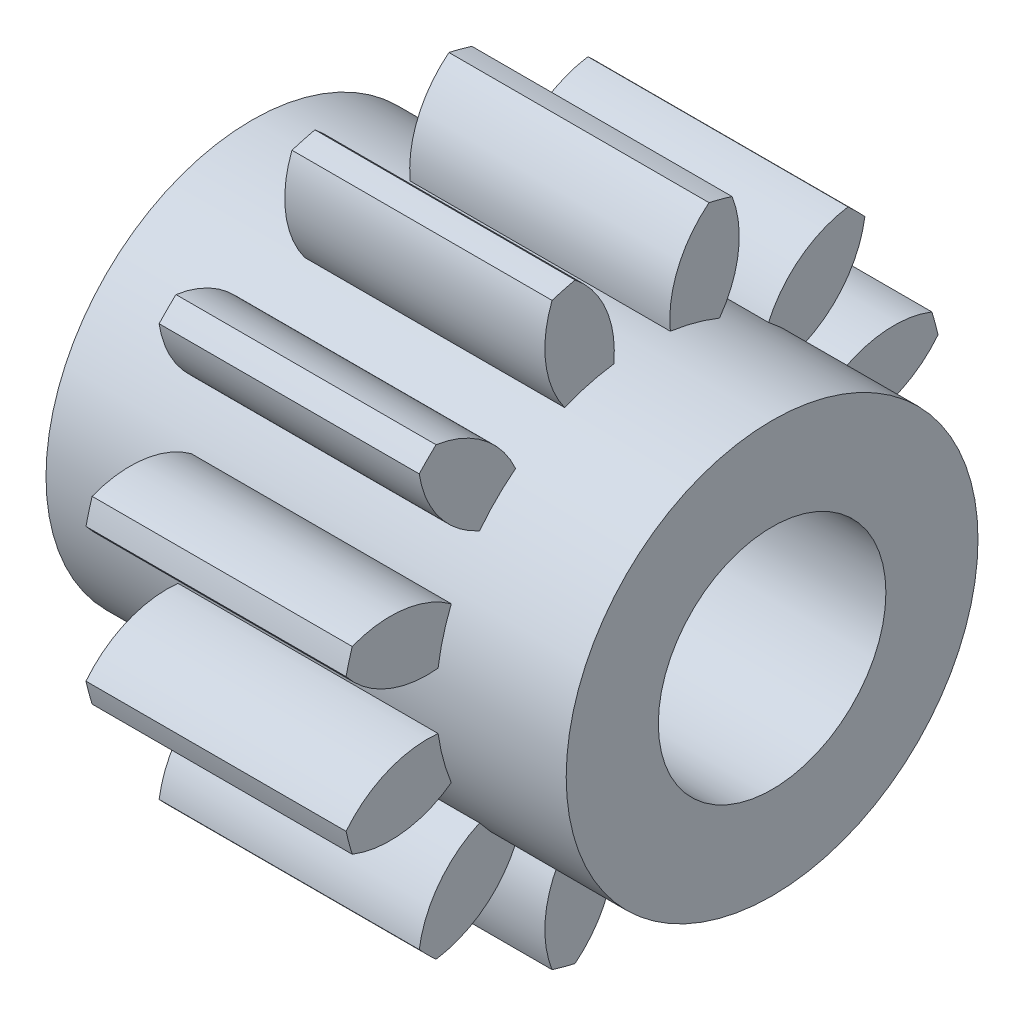
SolidWorks part; units mm, degrees
ref_plane "Plane1" through (0, 0, 0) normal (0, 0, 1) x (1, 0, 0)
ref_plane "Plane2" through (0, 0, 0) normal (0, 1, 0) x (1, 0, 0)
ref_plane "Plane3" through (0, 0, 0) normal (1, 0, 0) x (0, 0, -1)
sketch "HoldingSke" plane through (0, 0, 0) normal (0, 1, 0) x (1, 0, 0)
  line L0 (0, 0) -> (149.0697, -31.6857)
  line L1 (-15, 0) -> (100, 0) construction
  line L2 (0, 0) -> (-2.1039, 2.3779)
  line L3 (0, 0) -> (-11.863, 4.5341)
  line L4 (0, 0) -> (8.4473, 1.7955)
  line L5 (0, 0) -> (-47.5972, -17.7524)
  line L6 (0, 0) -> (-21.0557, -14.2063)
  line L7 (-2.1039, 2.3779) -> (8.8308, 51.9871)
  line L8 (-76.2, 54.61) -> (-51.7144, 54.61)
  line L9 (-67.7845, 28.3722) -> (-49.3413, 33.142)
  line L10 (-76.2, 71.12) -> (104.1128, 71.12)
  line L11 (0, 0) -> (-25.4, 0)
  line L12 (-76.2, 101.6) -> (-76.0298, 101.6)
  line L13 (24.9733, 27.94) -> (52.9518, 28.4284)
  line L14 (24.9733, 27.94) -> (24.9746, 27.94)
  line L15 (24.9733, 27.94) -> (100.4006, 29.5858)
  circle A0 centre (0, 0) radius 11.1125
  circle A1 centre (0, 0) radius 20.1071
  circle A2 centre (0, 0) radius 25.4
  circle A3 centre (0, 0) radius 11.1125
  dimension "MHD" = 40.2141
  dimension "Hub_dia" = 50.8
  dimension "Bore" = 22.225
  dimension "MBD" = 22.225
  dimension "Num_teeth" = 12
  dimension "Pitch" = 152.4
  dimension "Overall_len" = 50.8
  dimension "Show_teeth" = 12
  dimension "Thickness" = 25.4
  dimension "OAL" = 50.8001
  dimension "T_dim" = 24.4856
  dimension "Ap" = 14.5
  dimension "H" = 19.05
  dimension "Pitch_radius" = 180.3128
  dimension "Width" = 25.4
  dimension "Backlash" = 0.1702
  dimension "Addendum_fac" = 1
  dimension "Dedendum_fac" = 1.25
  dimension "Clearance_fac" = 0.25
  dimension "Dedendum_add" = 0.0013
sketch "BasProSke" plane through (0, 0, 0) normal (0, 1, 0) x (1, 0, 0)
  line L0 (-10, 0) -> (60, 0) construction
  line L1 (0, 0) -> (0, 29.6333)
  line L2 (0, 0) -> (25.4, 0)
  line L3 (25.4, 0) -> (25.4, 29.6333)
  line L4 (25.4, 29.6333) -> (0, 29.6333)
  dimension "Thickness" = 25.4
  dimension "Diameter" = 59.2667
revolve "Base-Revolve" add sketch "BasProSke" angle 360 about L0
sketch "TooCutSke" plane through (0, 0, 0) normal (1, 0, 0) x (0, 0, -1)
  line L1 (0, 0) -> (0, 107) construction
  line L2 (0, 0) -> (-3.6127, 25.1418) construction
  line L3 (0, 0) -> (-13.0549, 48.7215) construction
  line L4 (-3.6127, 25.1418) -> (-6.5274, 24.3608) construction
  arc A0 (2.7629, 19.9163) -> (-2.7629, 19.9163) centre (0, 0) ccw
  arc A1 (6.5664, 28.9227) -> (-6.5664, 28.9227) centre (0, 0) ccw
  circle A2 centre (0, 0) radius 25.4 construction
  circle A3 centre (0, 0) radius 24.591 construction
  arc A4 (-2.7629, 19.9163) -> (-6.5664, 28.9227) centre (-12.8697, 20.9544) ccw
  arc A5 (6.5664, 28.9227) -> (2.7629, 19.9163) centre (12.8697, 20.9544) ccw
  dimension "Root_dia" = 40.2141
  dimension "Overcut_dia" = 59.3175
  dimension "Pitch_dia" = 50.8
  dimension "Base_dia" = 49.1819
  dimension "Flank_rad" = 10.16
  dimension "Half_ang" = 15
  dimension "Half_CT" = 3.0176
extrude "ToothCut" cut sketch "TooCutSke" along normal through all
fillet "Breaks" [suppressed] radius 0.0847
fillet "RootFillets" [suppressed] radius 1.0596
pattern_circular "TeethCuts" count 12 every 30 about axis through (-10, 0, 0) along (1, 0, 0) of "ToothCut", "RootFillets", "Breaks"
sketch "HubNeaOneSke" plane through (0, 0, 0) normal (-1, 0, 0) x (0, 0, 1)
  circle A0 centre (0, 0) radius 20.1071
  dimension "Diameter" = 40.2141
extrude "HubNearOne" [suppressed] add sketch "HubNeaOneSke" along normal blind 25.4001
sketch "HubNeaBotSke" plane through (0, 0, 0) normal (-1, 0, 0) x (0, 0, 1)
  circle A0 centre (0, 0) radius 20.1071
  dimension "Diameter" = 40.2141
extrude "HubNearBoth" add sketch "HubNeaBotSke" along normal blind 12.7
ref_plane "FarPln" through (25.4, 0, 0) normal (1, 0, 0) x (0, 0, -1)
sketch "HubFarSke" plane through (25.4, 0, 0) normal (1, 0, 0) x (0, 0, -1)
  circle A0 centre (0, 0) radius 20.1071
  dimension "Diameter" = 40.2141
extrude "HubFar" add sketch "HubFarSke" along normal blind 12.7
sketch "BorSke" plane through (0, 0, 0) normal (1, 0, 0) x (0, 0, -1)
  circle A0 centre (0, 0) radius 11.1125
  dimension "Diameter" = 22.225
extrude "Bore" cut sketch "BorSke" along normal mid plane 101.6001
sketch "KeySke" plane through (0, 0, 0) normal (1, 0, 0) x (0, 0, -1)
  line L0 (-2.3812, 0) -> (-2.3812, 13.3731)
  line L1 (-2.3812, 13.3731) -> (2.3812, 13.3731)
  line L2 (2.3812, 13.3731) -> (2.3812, 0)
  line L3 (0, 0) -> (0, 34) construction
  line L4 (-2.3812, 0) -> (2.3812, 0)
  dimension "Offset" = 13.3731
  dimension "Width" = 4.7625
extrude "Keyway" [suppressed] cut sketch "KeySke" along normal mid plane 101.6001
pattern_circular "Keyway2" [suppressed] count 2 every 90 about axis through (-10, 0, 0) along (1, 0, 0)
sketch "Sketch1" [suppressed] plane through (25.4, 0, 0) normal (1, 0, 0) x (0, 0, -1)
  line L0 (0, 0) -> (-61.4073, -35.4535)
  line L1 (-61.4073, -35.4535) -> (-75.2078, -45.2777)
  line L3 (0.9665, 70.9005) -> (4.0387, 87.6924)
  arc A0 (-62.5405, -33.414) -> (-60.2076, -37.4547) centre (0, 0) ccw construction
  circle A1 centre (0, 0) radius 70.9071
  circle A2 centre (0, 0) radius 87.7854
sketch "Sketch3" [suppressed] plane through (25.4, 0, 0) normal (1, 0, 0) x (0, 0, -1)
  line L0 (-61.7691, -34.2346) -> (-76.8798, -41.9429)
  line L1 (0, 70.6217) -> (-2.474, 87.542)
  circle A0 centre (0, 0) radius 70.6217
  circle A1 centre (0, 0) radius 87.5769
extrude "Cut-Extrude2" [suppressed] cut sketch "Sketch3" against normal blind 50.8 contours L0 A1 L1 A0
scale "Scale1" scale about centroid uniform scaling yes scale factor 0.39
equation "' \"Pitch@HoldingSke\" = 4"
equation "' \"Num_teeth@HoldingSke\" = 12"
equation "' \"Ap@HoldingSke\" =  20"
equation "' \"Ap@HoldingSke\" = 20"
equation "' \"Width@HoldingSke\" = 0.5"
equation "' \"Hub_dia@HoldingSke\"= 1"
equation "' \"Hub_dia@HoldingSke\" = 1"
equation "' \"Overall_len@HoldingSke\" = 1.0"
equation "' \"Bore@HoldingSke\" = 0.75"
equation "' \"T_dim@HoldingSke\" = 0.85"
equation "' \"Width@KeySke\" = 0.25"
equation "' \"Show_teeth@HoldingSke\" = 13"
equation "' \"Backlash@HoldingSke\" = 0.009"
equation "' \"Addendum_fac@HoldingSke\" = 1.0"
equation "' \"Dedendum_fac@HoldingSke\" = 1.25"
equation "' \"Dedendum_add@HoldingSke\" = 0.00005"
equation "' \"Clearance_fac@HoldingSke\" = 0.25"
equation "' \"Pitch@HoldingSke\" = 0.5"
equation "' \"Num_teeth@HoldingSke\" = 23"
equation "' \"Show_teeth@HoldingSke\" = 23"
equation "' \"Backlash@HoldingSke\" = 0.0375"
equation "\"Overcut_dia@TooCutSke\" = (\"Num_teeth@HoldingSke\" + 2 * \"Addendum_fac@HoldingSke\") / \"Pitch@HoldingSke\" + 0.002"
equation "\"Pitch_dia@TooCutSke\" = \"Num_teeth@HoldingSke\" / \"Pitch@HoldingSke\""
equation "\"Base_dia@TooCutSke\" = \"Num_teeth@HoldingSke\" / \"Pitch@HoldingSke\" * cos((\"Ap@HoldingSke\"  * 3.14159265 / 180))"
equation "\"Root_dia@TooCutSke\" = (\"Num_teeth@HoldingSke\" + 2) / \"Pitch@HoldingSke\" - 2 * (\"Addendum_fac@HoldingSke\" + \"Dedendum_fac@HoldingSke\") / \"Pitch@HoldingSke\" - \"Dedendum_add@HoldingSke\" * 2"
equation "\"Half_ang@TooCutSke\" = 180 / \"Num_teeth@HoldingSke\""
equation "\"Half_CT@TooCutSke\" = \"Num_teeth@HoldingSke\" / \"Pitch@HoldingSke\" * sin((3.14159265 / 2 / \"Num_teeth@HoldingSke\")) / 2 - 7 * \"Backlash@HoldingSke\" / 4"
equation "\"Flank_rad@TooCutSke\" = \"Num_teeth@HoldingSke\" / \"Pitch@HoldingSke\" / 5"
equation "\"Radius@RootFillets\" = \"Clearance_fac@HoldingSke\" / \"Pitch@HoldingSke\" + \"Dedendum_add@HoldingSke\""
equation "\"Break_rad@Breaks\" = 0.02 / \"Pitch@HoldingSke\""
equation "\"Thickness@HoldingSke\" = \"Width@HoldingSke\""
equation "\"OAL@HoldingSke\" = \"Thickness@HoldingSke\""
equation "\"MHD@HoldingSke\" = (\"Num_teeth@HoldingSke\" + 2) / \"Pitch@HoldingSke\" - 2 * (\"Addendum_fac@HoldingSke\" + \"Dedendum_fac@HoldingSke\")  / \"Pitch@HoldingSke\" - \"Dedendum_add@HoldingSke\" * 2"
equation "\"MBD@HoldingSke\" = (\"Num_teeth@HoldingSke\" + 2) / \"Pitch@HoldingSke\" - 2 * (\"Addendum_fac@HoldingSke\" + \"Dedendum_fac@HoldingSke\")  / \"Pitch@HoldingSke\" - \"Dedendum_add@HoldingSke\" * 2 - 0.002"
equation "\"MHD@HoldingSke\" = ((sgn( \"MHD@HoldingSke\" - \"Hub_dia@HoldingSke\" )-1)*( \"MHD@HoldingSke\" - \"Hub_dia@HoldingSke\" ))/-2+ \"Hub_dia@HoldingSke\""
equation "\"MBD@HoldingSke\" = ((sgn( \"MBD@HoldingSke\" - \"Bore@HoldingSke\" )-1)*( \"MBD@HoldingSke\" - \"Bore@HoldingSke\" ))/-2+ \"Bore@HoldingSke\""
equation "\"OAL@HoldingSke\" = ((sgn( \"OAL@HoldingSke\" - \"Overall_len@HoldingSke\" )+1)*( \"OAL@HoldingSke\" - \"Overall_len@HoldingSke\" ))/2 + \"Overall_len@HoldingSke\" + 0.000002"
equation "\"Num_teeth@TeethCuts\" = int( \"Show_teeth@HoldingSke\" ) + 1"
equation "\"Num_teeth@TeethCuts\" = ((sgn( \"Num_teeth@TeethCuts\" - \"Num_teeth@HoldingSke\" )-1)*( \"Num_teeth@TeethCuts\" - \"Num_teeth@HoldingSke\" ))/-2+ \"Num_teeth@HoldingSke\""
equation "\"Num_teeth@TeethCuts\" = ((sgn( \"Num_teeth@TeethCuts\" - 2.0)+1)*( \"Num_teeth@TeethCuts\" - 2.0))/2 +2.0"
equation "\"Angle@TeethCuts\" = 360.0 / \"Num_teeth@HoldingSke\""
equation "\"Diameter@BasProSke\" = (\"Num_teeth@HoldingSke\" + 2 * \"Addendum_fac@HoldingSke\") / \"Pitch@HoldingSke\""
equation "\"Thickness@BasProSke\"  = \"Thickness@HoldingSke\""
equation "' \"Fillet_rad@BasProSke\" =  \"Thickness@HoldingSke\" * 0.05"
equation "' \"Fillet_rad@BasProSke\" = \"Thickness@HoldingSke\" * 0.05"
equation "\"MHD@HoldingSke\" = ((sgn( \"MHD@HoldingSke\" - \"Root_dia@TooCutSke\" )-1)*( \"MHD@HoldingSke\" - \"Root_dia@TooCutSke\" ))/-2+ \"Root_dia@TooCutSke\""
equation "\"Diameter@HubNeaOneSke\" = \"MHD@HoldingSke\""
equation "\"Length@HubNearOne\" = \"OAL@HoldingSke\" - \"Thickness@BasProSke\""
equation "\"Diameter@HubNeaBotSke\" = \"MHD@HoldingSke\""
equation "\"Length@HubNearBoth\" = ( \"OAL@HoldingSke\" - \"Thickness@BasProSke\" ) / 2.0"
equation "\"Thickness@FarPln\" = \"Thickness@BasProSke\""
equation "\"Diameter@HubFarSke\" = \"MHD@HoldingSke\""
equation "\"Length@HubFar\" = ( \"OAL@HoldingSke\" - \"Thickness@BasProSke\" ) / 2.0"
equation "\"Diameter@BorSke\" = \"MBD@HoldingSke\""
equation "\"D1@Bore\" = \"OAL@HoldingSke\" * 2.0"
equation "\"D1@Keyway\" = \"OAL@HoldingSke\" * 2.0"
equation "\"Offset@KeySke\" = \"T_dim@HoldingSke\" - \"MBD@HoldingSke\" / 2.0"
